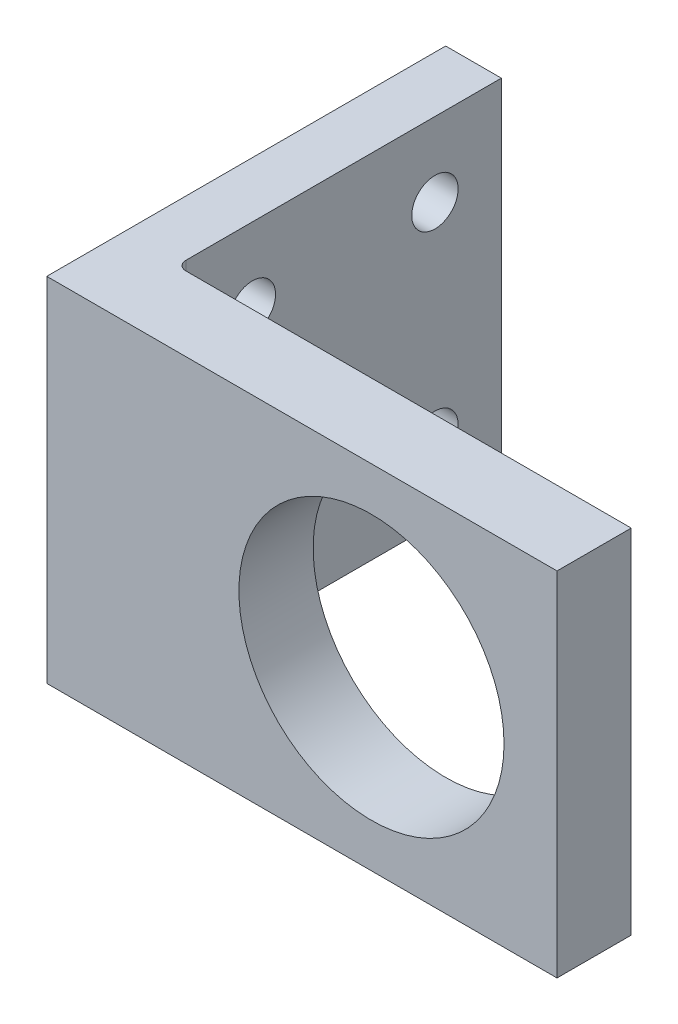
SolidWorks part; units mm, degrees
ref_plane "Piano frontale" through (0, 0, 0) normal (0, 0, 1) x (1, 0, 0)
ref_plane "Piano superiore" through (0, 0, 0) normal (0, 1, 0) x (1, 0, 0)
ref_plane "Piano destro" through (0, 0, 0) normal (1, 0, 0) x (0, 0, -1)
sketch "Sketch1" plane through (0, 0, 0) normal (0, 0, 1) x (1, 0, 0)
  line L0 (0, 19) -> (55, 19) construction
  line L1 (0, 0) -> (55, 0)
  line L2 (0, 0) -> (0, 38)
  line L3 (0, 38) -> (55, 38)
  line L4 (55, 0) -> (55, 38)
  circle A0 centre (35, 19) radius 14.2875
  point P9 (0, 0)
  point P10 (0, 0)
  dimension "D2" = 28.575
  dimension "D1" = 55
  dimension "D3" = 20
  dimension "D8" = 38
extrude "Boss-Extrude3" add sketch "Sketch1" along normal blind 8
sketch "Sketch8" plane through (0, 0, 0) normal (0, 0, -1) x (-1, 0, 0)
  line L0 (-55, 38) -> (0, 38) construction
  line L6 (0, 38) -> (0, 0) construction
  line L7 (-16.35, 19) -> (-35, 19) construction
  line L11 (-18.1947, 25) -> (-18.1947, 24.9954)
  line L12 (0, 0) -> (-55, 0) construction
  line L17 (0, 38) -> (-6, 38)
  line L18 (0, 38) -> (0, 0)
  line L19 (0, 0) -> (-6, 0)
  line L20 (-6, 38) -> (-6, 0)
  dimension "D1" = 6
extrude "Boss-Extrude6" add sketch "Sketch8" along normal blind 35
fillet "Fillet1" radius 1 1 edges at (6, 19, 0)
sketch "Sketch9" plane through (6, 0, 0) normal (1, 0, 0) x (0, 0, -1)
  line L0 (1, 38) -> (35, 0) construction
  line L1 (35, 38) -> (1, 0) construction
  line L2 (35, 38) -> (1, 38) construction
  line L3 (1, 19) -> (35, 19) construction
  line L4 (1, 38) -> (1, 0) construction
  line L5 (35, 38) -> (35, 0) construction
  line L6 (18, 38) -> (18, 0) construction
  line L7 (35, 0) -> (1, 0) construction
  circle A0 centre (8.1579, 30) radius 2.5
  circle A1 centre (8.1579, 8) radius 2.5
  circle A2 centre (27.8421, 8) radius 2.5
  circle A3 centre (27.8421, 30) radius 2.5
  dimension "D1" = 5
  dimension "D2" = 8
extrude "Cut-Extrude1" cut sketch "Sketch9" against normal blind 10
